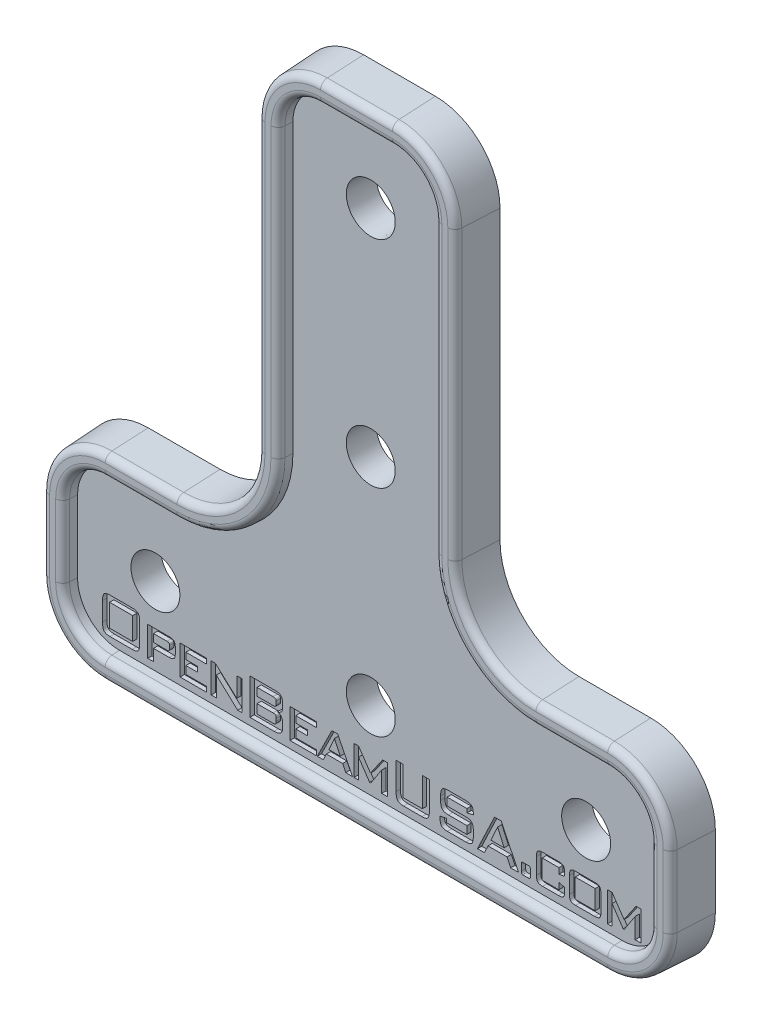
SolidWorks part; units mm, degrees
ref_plane "Front Plane" through (0, 0, 0) normal (0, 0, 1) x (1, 0, 0)
ref_plane "Top Plane" through (0, 0, 0) normal (0, 1, 0) x (1, 0, 0)
ref_plane "Right Plane" through (0, 0, 0) normal (1, 0, 0) x (0, 0, -1)
sketch "Sketch1" plane through (0, 0, 0) normal (0, 0, 1) x (1, 0, 0)
  line L0 (55, 0) -> (-55, 0) construction
  line L1 (-7.5, 30) -> (7.5, 30)
  line L2 (-7.5, 30) -> (-7.5, 0)
  line L3 (7.5, 0) -> (22.5, 0)
  line L4 (7.5, 30) -> (7.5, 0)
  line L5 (-22.5, 0) -> (-7.5, 0)
  line L6 (-22.5, 0) -> (-22.5, -15)
  line L7 (-22.5, -15) -> (22.5, -15)
  line L8 (22.5, 0) -> (22.5, -15)
  line L9 (0, 49.321) -> (0, -31.3726) construction
  line L10 (0, -54.6431) -> (0, 54.6431) construction
  dimension "D1" = 15
  dimension "D2" = 45
  dimension "D3" = 45
extrude "Boss-Extrude1" add sketch "Sketch1" along normal blind 2
fillet "Fillet1" radius 5 8 edges at (22.5, -15, 1) (22.5, 0, 1) (-7.5, 0, 1) (7.5, 0, 1) (7.5, 30, 1) (-22.5, -15, 1) (-22.5, 0, 1) (-7.5, 30, 1)
sketch "Sketch2" plane through (0, 0, 2) normal (0, 0, 1) x (1, 0, 0)
  line L0 (-22.5, -7.5) -> (22.5, -7.5) construction
  line L1 (-22.5, -5) -> (-22.5, -10) construction
  line L2 (22.5, -10) -> (22.5, -5) construction
  line L3 (0, 30) -> (0, -15) construction
  line L4 (2.5, 30) -> (-2.5, 30) construction
  line L5 (-17.5, -15) -> (17.5, -15) construction
  circle A0 centre (-15, -7.5) radius 1.6
  circle A1 centre (0, -7.5) radius 1.6
  circle A2 centre (15, -7.5) radius 1.6
  circle A3 centre (0, 22.5) radius 1.6
  circle A4 centre (0, 7.5) radius 1.6
  dimension "D1" = 3.2
  dimension "D2" = 15
  dimension "D3" = 15
  dimension "D4" = 15
  dimension "D5" = 15
extrude "Cut-Extrude1" cut sketch "Sketch2" against normal through all
other "Move Face1" face at (-9.4822, 1.9822, 1) face at (-15, 0, 1) face at (-20.5178, -1.9822, 1) face at (-22.5, -7.5, 1) face at (-20.5178, -13.0178, 1) face at (0, -15, 1) face at (20.5178, -13.0178, 1) face at (22.5, -7.5, 1) face at (20.5178, -1.9822, 1) face at (15, 0, 1) face at (9.4822, 1.9822, 1) face at (7.5, 15, 1) face at (5.5178, 28.0178, 1) face at (0, 30, 1) face at (-5.5178, 28.0178, 1) face at (-7.5, 15, 1) parameters "D1"=0.5
draft "Draft1" type of draft neutral plane draft angle 3 faces to draft 21 face at (16.6, -7.5, 0) face at (1.6, 22.5, 0) face at (1.6, 7.5, 0) face at (1.6, -7.5, 0) face at (-13.4, -7.5, 0) face at (-20.216, -2.284, 1) face at (-22, -7.5, 1) face at (-20.216, -12.716, 1) face at (0, -14.5, 1) face at (20.216, -12.716, 1) face at (22, -7.5, 1) face at (20.216, -2.284, 1) face at (15, -0.5, 1) face at (9.1805, 1.6805, 1) face at (7, 15, 1) face at (5.216, 27.716, 1) face at (0, 29.5, 1) face at (-5.216, 27.716, 1) face at (-7, 15, 1) face at (-9.1805, 1.6805, 1) face at (-15, -0.5, 1) neutral plane through (0, 0, 0) neutral plane normal (0, 0, -1) reverse direction yes parameters "D1"=3
sketch "Sketch4" plane through (0, 0, 2) normal (0, 0, 1) x (1, 0, 0)
  line L0 (-17.5, -12.9214) -> (17.5, -12.9214)
  line L1 (20.4214, -10) -> (20.4214, -5)
  line L2 (17.5, -2.0786) -> (12.5, -2.0786)
  line L3 (5.4214, 5) -> (5.4214, 25)
  line L4 (2.5, 27.9214) -> (-2.5, 27.9214)
  line L5 (-5.4214, 25) -> (-5.4214, 5)
  line L6 (-12.5, -2.0786) -> (-17.5, -2.0786)
  line L7 (-20.4214, -5) -> (-20.4214, -10)
  line L8 (-17.5, -14.3952) -> (17.5, -14.3952)
  line L9 (21.8952, -10) -> (21.8952, -5)
  line L10 (17.5, -0.6048) -> (12.5, -0.6048)
  line L11 (6.8952, 5) -> (6.8952, 25)
  line L12 (2.5, 29.3952) -> (-2.5, 29.3952)
  line L13 (-6.8952, 25) -> (-6.8952, 5)
  line L14 (-12.5, -0.6048) -> (-17.5, -0.6048)
  line L15 (-21.8952, -5) -> (-21.8952, -10)
  line L16 (-17.5, -14.3952) -> (17.5, -14.3952)
  line L17 (21.8952, -10) -> (21.8952, -5)
  line L18 (17.5, -0.6048) -> (12.5, -0.6048)
  line L19 (6.8952, 5) -> (6.8952, 25)
  line L20 (2.5, 29.3952) -> (-2.5, 29.3952)
  line L21 (-6.8952, 25) -> (-6.8952, 5)
  line L22 (-12.5, -0.6048) -> (-17.5, -0.6048)
  line L23 (-21.8952, -5) -> (-21.8952, -10)
  arc A2 (17.5, -12.9214) -> (20.4214, -10) centre (17.5, -10) ccw
  arc A3 (20.4214, -5) -> (17.5, -2.0786) centre (17.5, -5) ccw
  arc A4 (5.4214, 5) -> (12.5, -2.0786) centre (12.5, 5) ccw
  arc A5 (5.4214, 25) -> (2.5, 27.9214) centre (2.5, 25) ccw
  arc A6 (-2.5, 27.9214) -> (-5.4214, 25) centre (-2.5, 25) ccw
  arc A7 (-12.5, -2.0786) -> (-5.4214, 5) centre (-12.5, 5) ccw
  arc A8 (-17.5, -2.0786) -> (-20.4214, -5) centre (-17.5, -5) ccw
  arc A9 (-20.4214, -10) -> (-17.5, -12.9214) centre (-17.5, -10) ccw
  arc A10 (17.5, -14.3952) -> (21.8952, -10) centre (17.5, -10) ccw
  arc A11 (21.8952, -5) -> (17.5, -0.6048) centre (17.5, -5) ccw
  arc A12 (6.8952, 5) -> (12.5, -0.6048) centre (12.5, 5) ccw
  arc A13 (6.8952, 25) -> (2.5, 29.3952) centre (2.5, 25) ccw
  arc A14 (-2.5, 29.3952) -> (-6.8952, 25) centre (-2.5, 25) ccw
  arc A15 (-12.5, -0.6048) -> (-6.8952, 5) centre (-12.5, 5) ccw
  arc A16 (-17.5, -0.6048) -> (-21.8952, -5) centre (-17.5, -5) ccw
  arc A17 (-21.8952, -10) -> (-17.5, -14.3952) centre (-17.5, -10) ccw
  arc A18 (17.5, -14.3952) -> (21.8952, -10) centre (17.5, -10) ccw
  arc A19 (21.8952, -5) -> (17.5, -0.6048) centre (17.5, -5) ccw
  arc A20 (6.8952, 5) -> (12.5, -0.6048) centre (12.5, 5) ccw
  arc A21 (6.8952, 25) -> (2.5, 29.3952) centre (2.5, 25) ccw
  arc A22 (-2.5, 29.3952) -> (-6.8952, 25) centre (-2.5, 25) ccw
  arc A23 (-12.5, -0.6048) -> (-6.8952, 5) centre (-12.5, 5) ccw
  arc A24 (-17.5, -0.6048) -> (-21.8952, -5) centre (-17.5, -5) ccw
  arc A25 (-21.8952, -10) -> (-17.5, -14.3952) centre (-17.5, -10) ccw
  dimension "D1" = 0
extrude "Boss-Extrude3" add sketch "Sketch4" along normal blind 1 draft 3
fillet "Fillet3" radius 0.5 32 edges at (-7.5317, 0.0317, 3) (-5.4738, 15, 3) (-4.6028, 27.1028, 3) (0, 27.9738, 3) (4.6028, 27.1028, 3) (5.4738, 15, 3) (7.5317, 0.0317, 3) (15, -2.0262, 3) (19.6028, -2.8972, 3) (20.4738, -7.5, 3) (19.6028, -12.1028, 3) (0, -12.9738, 3) (-19.6028, -12.1028, 3) (-20.4738, -7.5, 3) (-19.6028, -2.8972, 3) (-8.4997, 0.9997, 3) (-6.8428, 15, 3) (-5.5708, 28.0708, 3) (0, 29.3428, 3) (5.5708, 28.0708, 3) (6.8428, 15, 3) (8.4997, 0.9997, 3) (15, -0.6572, 3) (20.5708, -1.9292, 3) (21.8428, -7.5, 3) (20.5708, -13.0708, 3) (0, -14.3428, 3) (-20.5708, -13.0708, 3) (-21.8428, -7.5, 3) (-20.5708, -1.9292, 3) (-15, -2.0262, 3) (-15, -0.6572, 3)
sketch "Sketch5" plane through (0, 0, 0) normal (0, 0, -1) x (-1, 0, 0)
  line L0 (0, 54.6431) -> (0, -54.6431) construction
  line L1 (-14.5, -13.8) -> (14.5, -13.8)
  line L2 (-15, -13.3) -> (-15, -10.3)
  line L3 (-14.5, -9.8) -> (14.5, -9.8)
  line L4 (15, -13.3) -> (15, -10.3)
  line L5 (-15, -13.8) -> (15, -9.8) construction
  line L6 (-15, -9.8) -> (15, -13.8) construction
  line L7 (17.5, -14.5) -> (-17.5, -14.5) construction
  arc A0 (14.5, -13.8) -> (15, -13.3) centre (14.5, -13.3) ccw
  arc A1 (14.5, -9.8) -> (15, -10.3) centre (14.5, -10.3) cw
  arc A2 (-14.5, -13.8) -> (-15, -13.3) centre (-14.5, -13.3) cw
  arc A3 (-15, -10.3) -> (-14.5, -9.8) centre (-14.5, -10.3) cw
  point P0 (0, -11.8)
  dimension "D4" = 0.5
  dimension "D1" = 30
  dimension "D2" = 4
  dimension "D3" = 0.7
extrude "Cut-Extrude2" cut sketch "Sketch5" against normal blind 0.2 draft 3
sketch "Sketch6" plane through (0, 0, 2) normal (0, 0, 1) x (1, 0, 0)
  line L0 (-19.1832, -12.4214) -> (19.1832, -12.4214) construction
  line L3 (-17.5, -12.9214) -> (17.5, -12.9214) construction
  arc A0 (17.5, -12.949) -> (20.449, -10) centre (17.5, -10) ccw construction
  arc A1 (-20.449, -10) -> (-17.5, -12.949) centre (-17.5, -10) ccw construction
  text T0 "OpenBeamUSA.com" font "BankGothic Md BT" height 2.5
  dimension "D1" = 0.5
extrude "Cut-Extrude3" cut sketch "Sketch6" against normal blind 0.3
sketch "Sketch7" plane through (0, 0, 0) normal (0, 0, -1) x (-1, 0, 0)
  line L0 (-14.9895, -11.8) -> (14.9895, -11.8) construction
  line L2 (14.9895, -13.3) -> (14.9895, -10.3) construction
  text T0 "TL625-000101-002\r\n" font "Arial Narrow" height 1.5
  text T1 ">>PA66 + 30GF <<" font "Arial Narrow" height 1
split line "Split Line1"
sketch "Alignment_Sketch" plane through (0, 0, 0) normal (0, 0, -1) x (-1, 0, 0)
  line L0 (0, 22.5) -> (0, -7.5) construction
  line L1 (-15, -7.5) -> (15, -7.5) construction
  point P0 (-15, -7.5)
  point P1 (0, -7.5)
  point P3 (15, -7.5)
  point P5 (0, 7.5)
  point P7 (0, 22.5)
